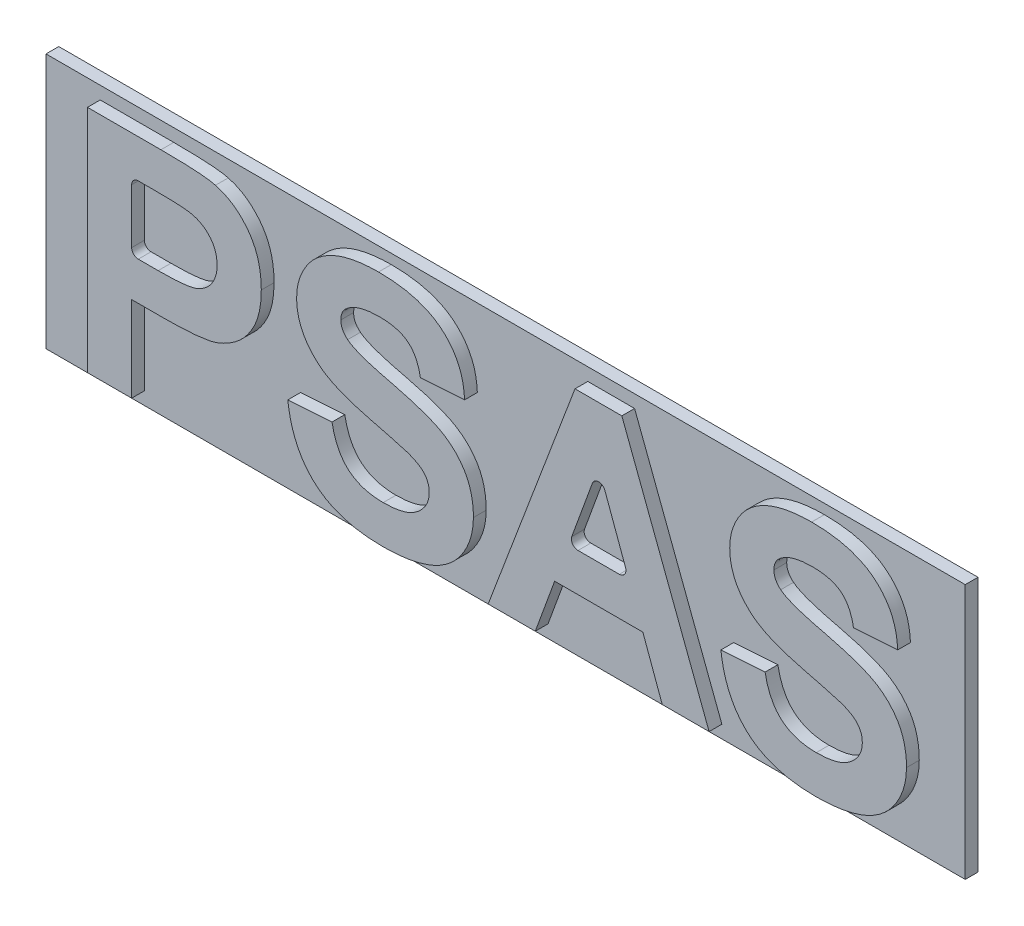
SolidWorks part; units mm, degrees
ref_plane "Front Plane" through (0, 0, 0) normal (0, 0, 1) x (1, 0, 0)
ref_plane "Top Plane" through (0, 0, 0) normal (0, 1, 0) x (1, 0, 0)
ref_plane "Right Plane" through (0, 0, 0) normal (1, 0, 0) x (0, 0, -1)
sketch "Sketch1" plane through (0, 0, 0) normal (0, 0, 1) x (1, 0, 0)
  line L1 (-114.3, -31.75) -> (114.3, -31.75)
  line L2 (-114.3, -31.75) -> (-114.3, 31.75)
  line L3 (-114.3, 31.75) -> (114.3, 31.75)
  line L4 (114.3, -31.75) -> (114.3, 31.75)
  line L5 (-114.3, -31.75) -> (114.3, 31.75) construction
  line L6 (-114.3, 31.75) -> (114.3, -31.75) construction
  point P0 (0, 0)
  dimension "D1" = 63.5
  dimension "D2" = 228.6
extrude "Boss-Extrude1" add sketch "Sketch1" along normal blind 6.35
sketch "Sketch2" plane through (0, 0, 6.35) normal (0, 0, 1) x (1, 0, 0)
  line L2 (-114.3, -31.75) -> (114.3, -31.75) construction
  text T0 "PSAS" font "Arial" height 57.15
  dimension "D1" = 3.175
  dimension "D2" = 106.68
extrude "Cut-Extrude1" cut sketch "Sketch2" against normal blind 3.175 flip side to cut
sketch "Sketch3" plane through (-114.3, 0, 0) normal (-1, 0, 0) x (0, 0, 1)
  line L0 (0, 31.75) -> (31.75, 31.75) construction
  dimension "D1" = 31.75
fillet "Fillet1" radius 1.651 5 edges at (-89.8281, 2.1981, 4.7625) (-89.8281, 19.05, 4.7625) (18.8165, -5.8615, 4.7625) (33.8137, -5.8615, 4.7625) (26.3037, 14.6538, 4.7625)
